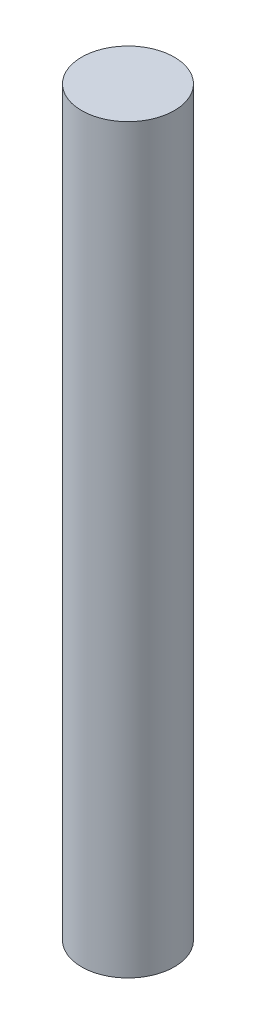
SolidWorks part; units mm, degrees
ref_plane "Front Plane" through (0, 0, 0) normal (0, 0, 1) x (1, 0, 0)
ref_plane "Top Plane" through (0, 0, 0) normal (0, 1, 0) x (1, 0, 0)
ref_plane "Right Plane" through (0, 0, 0) normal (1, 0, 0) x (0, 0, -1)
sketch "Sketch1" plane through (0, 0, 0) normal (0, 1, 0) x (1, 0, 0)
  circle A0 centre (0, 0) radius 1.5875
  dimension "D1" = 3.175
extrude "Boss-Extrude1" add sketch "Sketch1" along normal blind 25.4
